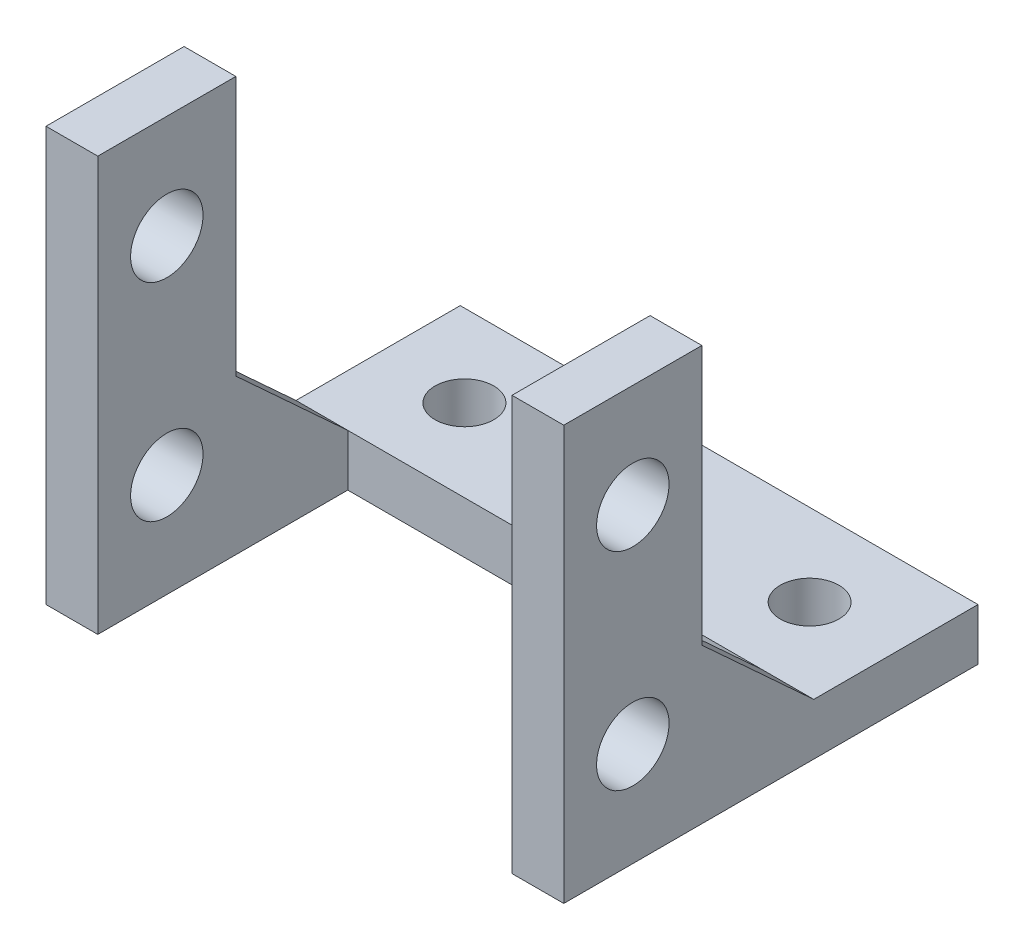
SolidWorks part; units mm, degrees
ref_plane "Front Plane" through (0, 0, 0) normal (0, 0, 1) x (1, 0, 0)
ref_plane "Top Plane" through (0, 0, 0) normal (0, 1, 0) x (1, 0, 0)
ref_plane "Right Plane" through (0, 0, 0) normal (1, 0, 0) x (0, 0, -1)
sketch "Sketch1" plane through (0, 0, 0) normal (1, 0, 0) x (0, 0, -1)
  line L0 (0, 0) -> (24, 0)
  line L1 (24, 0) -> (24, 3)
  line L5 (8, 24) -> (0, 24)
  line L6 (0, 24) -> (0, 0)
  line L7 (0, 12) -> (8, 12) construction
  line L8 (8, 24) -> (8, 8.9609)
  line L11 (8, 8.9609) -> (14.4839, 3)
  line L12 (14.4839, 3) -> (24, 3)
  circle A0 centre (4, 6) radius 2.1
  circle A1 centre (4, 18) radius 2.1
  point P5 (8, 7.5959)
  point P6 (8, 8.158)
  point P12 (14.4839, 3)
  point P13 (4, 12)
  point P16 (12, 0)
  point P18 (8, 9.523)
  point P19 (8, 8.9609)
  dimension "D4" = 4.2
  dimension "D1" = 24
  dimension "D2" = 8
  dimension "D3" = 24
  dimension "D5" = 12
  dimension "D6" = 3
extrude "Boss-Extrude1" add sketch "Sketch1" along normal mid plane 30
sketch "Sketch2" plane through (0, 0, 0) normal (0, 0, 1) x (1, 0, 0)
  line L0 (0, -1000) -> (0, 49000) construction
  line L1 (15, 24) -> (-15, 24) construction
  line L2 (-12, 0) -> (12, 0)
  line L3 (-12, 0) -> (-12, 24)
  line L4 (-12, 24) -> (12, 24)
  line L5 (12, 0) -> (12, 24)
  line L6 (-12, 0) -> (12, 24) construction
  line L7 (-12, 24) -> (12, 0) construction
  line L9 (15, 8.9609) -> (15, 24) construction
  line L10 (15, 0) -> (-15, 0) construction
  point P1 (0, 12)
  dimension "D1" = 3
extrude "Cut-Extrude3" cut sketch "Sketch2" against normal up to vertex
sketch "Sketch3" plane through (0, 0, 0) normal (0, 1, 0) x (1, 0, 0)
  line L0 (-15, 19.242) -> (15, 19.242) construction
  line L1 (-15, 24) -> (-15, 14.4839) construction
  line L2 (15, 24) -> (15, 14.4839) construction
  line L3 (0, 14.4839) -> (0, 24) construction
  line L4 (12, 14.4839) -> (-12, 14.4839) construction
  line L5 (15, 24) -> (-15, 24) construction
  circle A0 centre (-10, 19.242) radius 1.7
  circle A1 centre (10, 19.242) radius 1.7
  dimension "D1" = 3.4
  dimension "D2" = 20
extrude "Cut-Extrude4" cut sketch "Sketch3" along normal up to next
